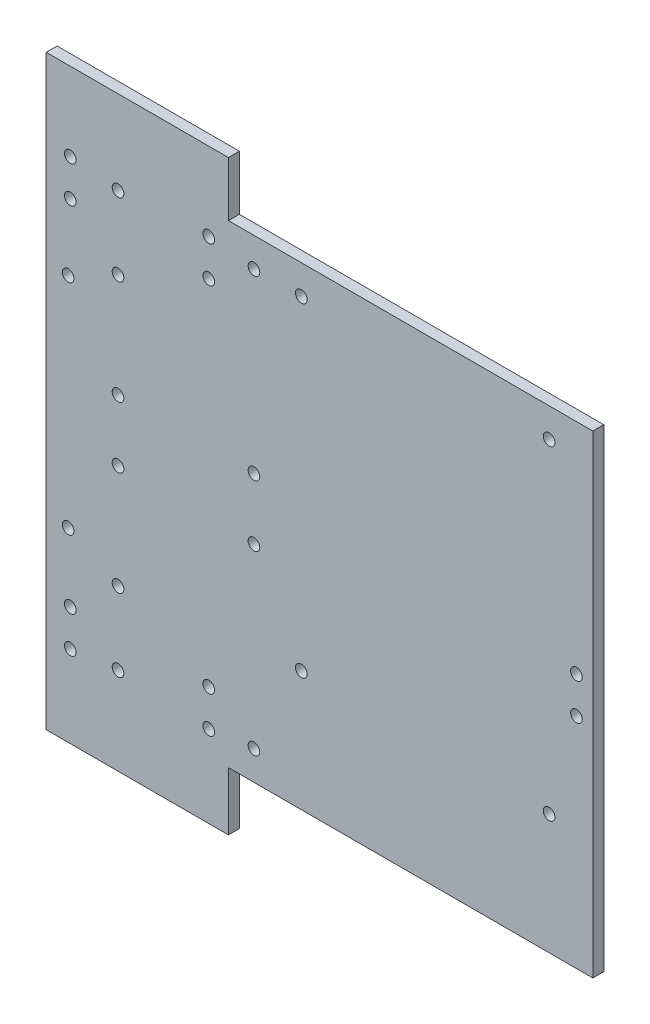
SolidWorks part; units mm, degrees
ref_plane "Front Plane" through (0, 0, 0) normal (0, 0, 1) x (1, 0, 0)
ref_plane "Top Plane" through (0, 0, 0) normal (0, 1, 0) x (1, 0, 0)
ref_plane "Right Plane" through (0, 0, 0) normal (1, 0, 0) x (0, 0, -1)
sketch "Sketch1" plane through (0, 0, 0) normal (0, 0, 1) x (1, 0, 0)
  line L1 (-75, -65) -> (75, -65)
  line L2 (-75, -65) -> (-75, 65)
  line L3 (-75, 65) -> (75, 65)
  line L4 (75, -65) -> (75, 65)
  line L5 (-75, -65) -> (75, 65) construction
  line L6 (-75, 65) -> (75, -65) construction
  point P0 (0, 0)
  dimension "D1" = 150
  dimension "D2" = 130
extrude "Boss-Extrude1" add sketch "Sketch1" along normal blind 3
sketch "Sketch2" plane through (0, 0, 3) normal (0, 0, 1) x (1, 0, 0)
  line L2 (75, 65) -> (-75, 65) construction
  line L3 (75, -65) -> (75, 65) construction
  line L4 (-75, -65) -> (75, -65) construction
  line L5 (-13, 62) -> (-13, 3.4) construction
  line L6 (-13, 3.4) -> (-60.3, 3.4) construction
  line L7 (-60.3, 3.4) -> (-60.3, 62) construction
  line L8 (-60.3, 62) -> (-13, 62) construction
  line L9 (0, 0) -> (-282.0509, 0) construction
  line L10 (-36.65, 3.4) -> (-36.65, 62) construction
  line L11 (-13, 32.7) -> (-60.3, 32.7) construction
  line L12 (11.576, 53.5) -> (-92.9014, 53.5) construction
  line L13 (-75, 65) -> (-75, -65) construction
  circle A0 centre (63, 57) radius 1.6
  circle A1 centre (70.5, 5) radius 1.6
  circle A2 centre (-5, 57) radius 1.6
  circle A3 centre (-5, -32) radius 1.6
  circle A4 centre (63, -32) radius 1.6
  circle A5 centre (70.5, -5) radius 1.6
  circle A6 centre (-18, 57) radius 1.6
  circle A8 centre (-18, 8.4) radius 1.6
  circle A9 centre (-55.3, 8.4) radius 1.6
  circle A10 centre (-55.3, 57) radius 1.6
  circle A11 centre (-18, -57) radius 1.6
  circle A12 centre (-55.3, -57) radius 1.6
  circle A13 centre (-55.3, -8.4) radius 1.6
  circle A14 centre (-18, -8.4) radius 1.6
  circle A15 centre (-30.4, 58.5) radius 1.6
  circle A16 centre (-68.4, 58.5) radius 1.6
  circle A17 centre (-68.4, 48.5) radius 1.6
  circle A18 centre (-30.4, 48.5) radius 1.6
  circle A19 centre (-68.4, -48.5) radius 1.6
  circle A20 centre (-68.4, -58.5) radius 1.6
  circle A21 centre (-30.4, -58.5) radius 1.6
  circle A22 centre (-30.4, -48.5) radius 1.6
  circle A23 centre (-69, -30) radius 1.6
  circle A25 centre (-69, 30) radius 1.6
  circle A26 centre (-55.3, 37) radius 1.6
  circle A27 centre (-55.3, -37) radius 1.6
  dimension "D1" = 3.2
  dimension "D4" = 3.2
  dimension "D5" = 3.2
  dimension "D6" = 3.2
  dimension "D9" = 3.2
  dimension "D15" = 3.2
  dimension "D20" = 3.2
  dimension "D25" = 13
  dimension "D28" = 3.2
  dimension "D29" = 3.2
  dimension "D33" = 3.2
  dimension "D34" = 6
  dimension "D36" = 3.2
  dimension "D2" = 8
  dimension "D3" = 12
  dimension "D7" = 12
  dimension "D8" = 89
  dimension "D10" = 8
  dimension "D11" = 68
  dimension "D12" = 89
  dimension "D13" = 68
  dimension "D14" = 4.5
  dimension "D16" = 4.5
  dimension "D17" = 10
  dimension "D18" = 60
  dimension "D19" = 58.6
  dimension "D21" = 8
  dimension "D22" = 47.3
  dimension "D23" = 5
  dimension "D24" = 5
  dimension "D26" = 6.25
  dimension "D27" = 38
  dimension "D30" = 6.5
  dimension "D31" = 6.5
  dimension "D32" = 5
  dimension "D35" = 30
  dimension "D37" = 25
  dimension "D38" = 5
extrude "Cut-Extrude1" cut sketch "Sketch2" against normal blind 23
sketch "Sketch3" plane through (0, 0, 0) normal (0, 0, -1) x (-1, 0, 0)
  line L0 (75, 65) -> (75, 80)
  line L1 (75, 80) -> (25, 80)
  line L2 (25, 80) -> (25, 65)
  line L3 (-75, 65) -> (75, 65) construction
  line L4 (75, -65) -> (75, -81)
  line L5 (75, -81) -> (25, -81)
  line L6 (25, -81) -> (25, -65)
  line L7 (75, -65) -> (-75, -65) construction
  line L8 (25, 65) -> (75, 65)
  line L9 (25, -65) -> (75, -65)
  dimension "D1" = 50
  dimension "D2" = 15
  dimension "D3" = 50
  dimension "D4" = 16
extrude "Boss-Extrude2" add sketch "Sketch3" against normal blind 3
equation "\"30э\"=3"
